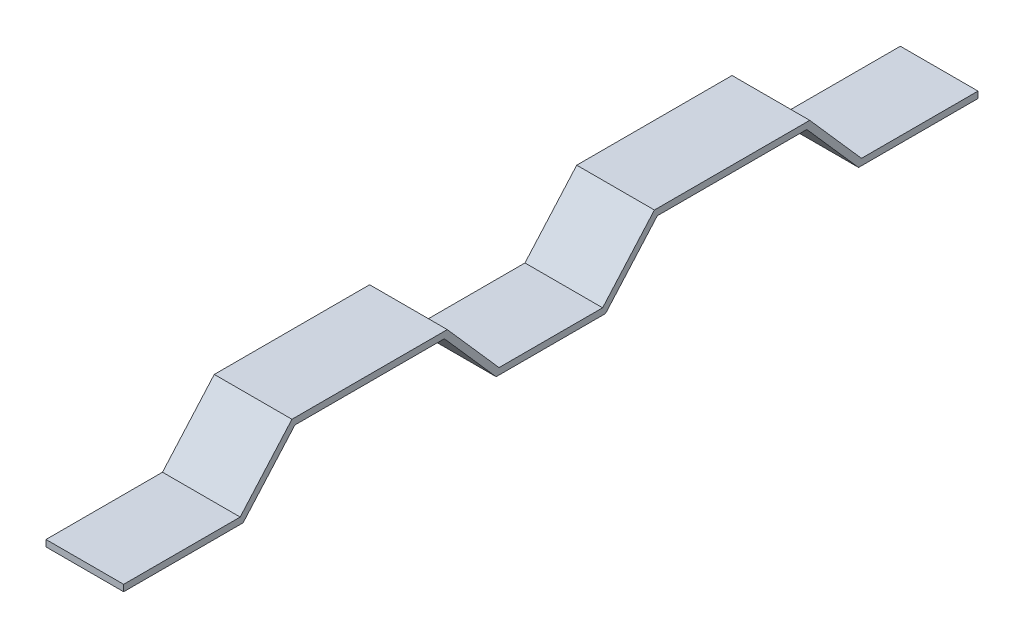
SolidWorks part; units mm, degrees
ref_plane "Front" through (0, 0, 0) normal (0, 0, 1) x (1, 0, 0)
ref_plane "Top" through (0, 0, 0) normal (0, 1, 0) x (1, 0, 0)
ref_plane "Right" through (0, 0, 0) normal (1, 0, 0) x (0, 0, -1)
sketch "Sketch1" plane through (0, 0, 0) normal (1, 0, 0) x (0, 0, -1)
  line L0 (-174.4636, 0) -> (-117.3136, 0)
  line L1 (-117.3136, 0) -> (-91.9136, 28.8441)
  line L2 (-91.9136, 28.8441) -> (-15.7136, 28.8441)
  line L3 (-15.7136, 28.8441) -> (9.6864, 0)
  line L4 (9.6864, 0) -> (60.4864, 0)
  line L5 (60.4864, 0) -> (85.8864, 28.8441)
  line L6 (85.8864, 28.8441) -> (162.0864, 28.8441)
  line L7 (162.0864, 28.8441) -> (187.4864, 0)
  line L8 (187.4864, 0) -> (244.6364, 0)
  line L9 (-174.4636, -3.175) -> (-115.8789, -3.175)
  line L10 (-115.8789, -3.175) -> (-90.4789, 25.6691)
  line L11 (-90.4789, 25.6691) -> (-17.1482, 25.6691)
  line L12 (-17.1482, 25.6691) -> (8.2518, -3.175)
  line L13 (8.2518, -3.175) -> (61.9211, -3.175)
  line L14 (61.9211, -3.175) -> (87.3211, 25.6691)
  line L15 (87.3211, 25.6691) -> (160.6518, 25.6691)
  line L16 (160.6518, 25.6691) -> (186.0518, -3.175)
  line L17 (186.0518, -3.175) -> (244.6364, -3.175)
  line L18 (-174.4636, -3.175) -> (-174.4636, 0)
  line L19 (244.6364, -3.175) -> (244.6364, 0)
  dimension "D1" = 76.2
  dimension "D2" = 76.2
  dimension "D3" = 50.8
  dimension "D4" = 158.75
  dimension "D5" = 158.75
  dimension "D6" = 25.4
  dimension "D7" = 25.4
  dimension "D8" = 25.4
  dimension "D9" = 25.4
  dimension "D10" = 3.175
extrude "Boss-Extrude1" add sketch "Sketch1" along normal blind 38.1
